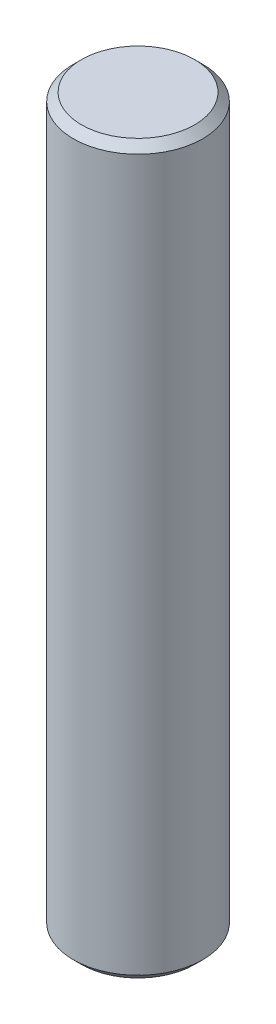
SolidWorks part; units mm, degrees
ref_plane "Front Plane" through (0, 0, 0) normal (0, 0, 1) x (1, 0, 0)
ref_plane "Top Plane" through (0, 0, 0) normal (0, 1, 0) x (1, 0, 0)
ref_plane "Right Plane" through (0, 0, 0) normal (1, 0, 0) x (0, 0, -1)
ref_plane "Plane1" through (0, 0, 6) normal (0, 0, 1) x (1, 0, 0)
sketch "Sketch1" plane through (0, 0, 6) normal (0, 0, 1) x (1, 0, 0)
  line L0 (28.5, 34) -> (25, 34)
  line L1 (25, 34) -> (25, -11)
  line L2 (25, -11) -> (28.5, -11)
  line L3 (28.5, -11) -> (29, -10.5)
  line L4 (29, -10.5) -> (29, 33.5)
  line L5 (29, 33.5) -> (28.5, 34)
  line L6 (25, 34) -> (25, -11) construction
revolve "Revolve1" add sketch "Sketch1" angle 360 about L6
